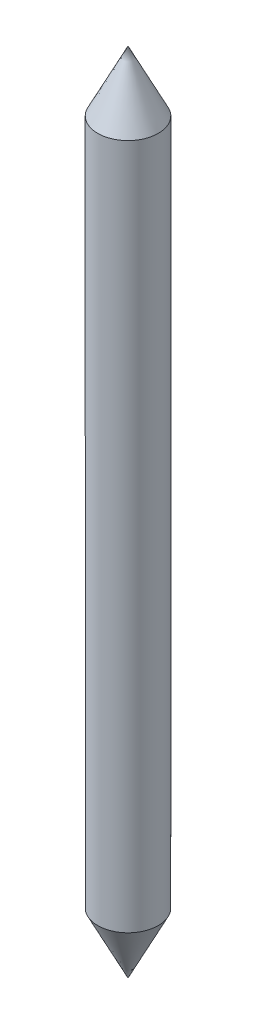
SolidWorks part; units mm, degrees
ref_plane "Alzado" through (0, 0, 0) normal (0, 0, 1) x (1, 0, 0)
ref_plane "Planta" through (0, 0, 0) normal (0, 1, 0) x (1, 0, 0)
ref_plane "Vista lateral" through (0, 0, 0) normal (1, 0, 0) x (0, 0, -1)
sketch "Croquis1" plane through (0, 0, 0) normal (0, 0, 1) x (1, 0, 0)
  line L0 (-1.8687, 16.7063) -> (-1.8687, 26.7063) construction
  line L1 (-1.8687, 16.7063) -> (-1.4937, 17.4563)
  line L2 (-1.4937, 17.4563) -> (-1.4937, 25.9563)
  line L3 (-1.4937, 25.9563) -> (-1.8687, 26.7063)
  line L4 (-1.8687, 16.7063) -> (-1.8687, 26.7063)
  dimension "D1" = 10
  dimension "D2" = 8.5
  dimension "D3" = 0.75
  dimension "D4" = 0.375
revolve "Revolución1" add sketch "Croquis1" angle 360 about L0
